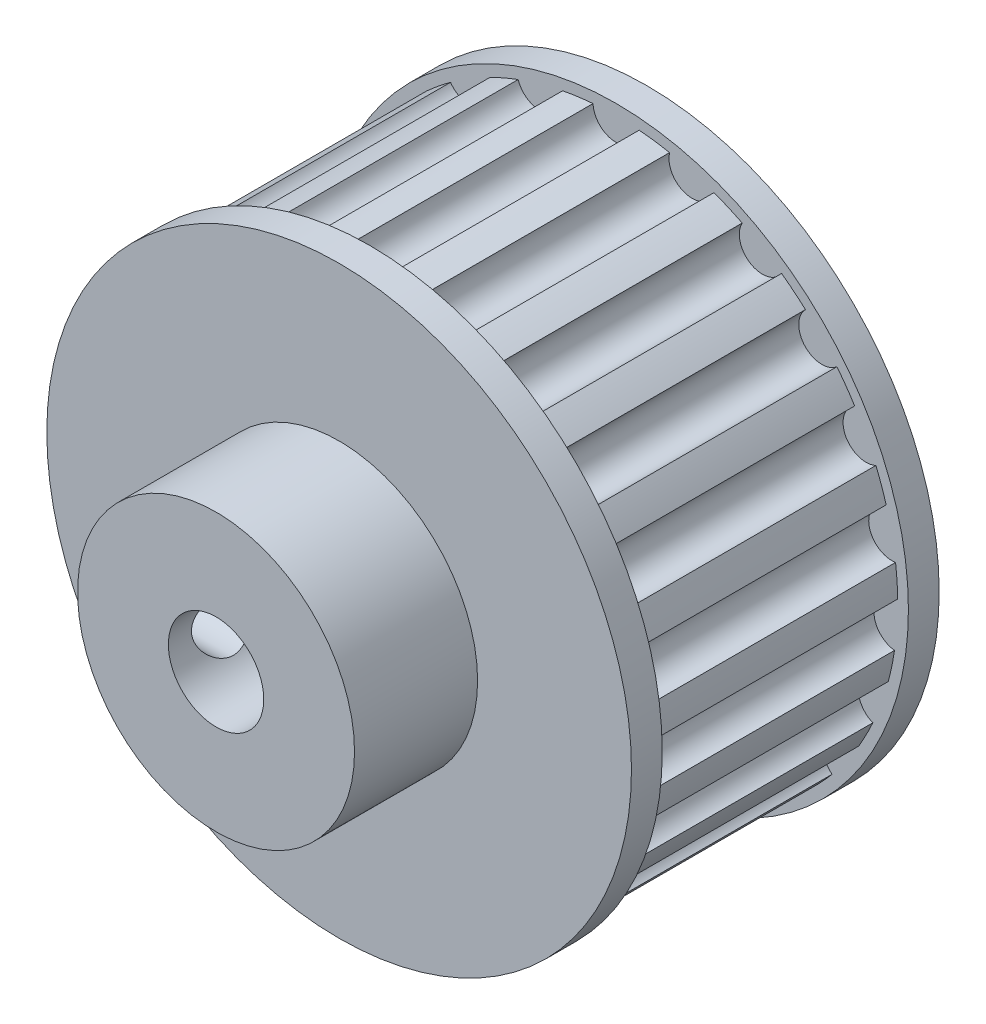
SolidWorks part; units mm, degrees
ref_plane "Спереди" through (0, 0, 0) normal (0, 0, 1) x (1, 0, 0)
ref_plane "Сверху" through (0, 0, 0) normal (0, 1, 0) x (1, 0, 0)
ref_plane "Справа" through (0, 0, 0) normal (1, 0, 0) x (0, 0, -1)
sketch "Эскиз1" plane through (0, 0, 0) normal (0, 0, 1) x (1, 0, 0)
  arc A0 (-1.4987, 18.241) -> (-3.4782, 17.969) centre (0, 0) ccw
  arc A1 (-1.4987, 18.241) -> (1.4987, 18.241) centre (0, 18.3025) ccw
  arc A2 (3.4782, 17.969) -> (6.3645, 17.1603) centre (4.938, 17.6238) ccw
  arc A3 (8.1972, 16.3642) -> (10.7583, 14.8068) centre (9.5097, 15.638) ccw
  arc A4 (12.3082, 13.5458) -> (14.3542, 11.3551) centre (13.3761, 12.4924) ccw
  arc A5 (15.5064, 9.7228) -> (16.8855, 7.0614) centre (16.2505, 8.4203) ccw
  arc A6 (17.5546, 5.1786) -> (18.1644, 2.2439) centre (17.9197, 3.7238) ccw
  arc A7 (18.3008, 0.2504) -> (18.0962, -2.7401) centre (18.2598, -1.249) ccw
  arc A8 (17.6897, -4.6963) -> (16.6859, -7.5208) centre (17.2457, -6.1291) ccw
  arc A9 (15.7667, -9.2948) -> (14.0381, -11.7437) centre (14.9526, -10.5547) ccw
  arc A10 (12.6743, -13.2039) -> (10.3491, -15.0956) centre (11.5505, -14.1975) ccw
  arc A11 (8.6419, -16.1338) -> (5.8926, -17.328) centre (7.2917, -16.7873) ccw
  arc A12 (3.9686, -17.8671) -> (0.999, -18.2752) centre (2.4922, -18.132) ccw
  arc A13 (-0.999, -18.2752) -> (-3.9686, -17.8671) centre (-2.4922, -18.132) ccw
  arc A14 (-5.8926, -17.328) -> (-8.6419, -16.1338) centre (-7.2917, -16.7873) ccw
  arc A15 (-10.3491, -15.0956) -> (-12.6743, -13.2039) centre (-11.5505, -14.1975) ccw
  arc A16 (-14.0381, -11.7437) -> (-15.7667, -9.2948) centre (-14.9526, -10.5547) ccw
  arc A17 (-16.6859, -7.5208) -> (-17.6897, -4.6963) centre (-17.2457, -6.1291) ccw
  arc A18 (-18.0962, -2.7401) -> (-18.3008, 0.2504) centre (-18.2598, -1.249) ccw
  arc A19 (-18.1644, 2.2439) -> (-17.5546, 5.1786) centre (-17.9197, 3.7238) ccw
  arc A20 (3.4782, 17.969) -> (1.4987, 18.241) centre (0, 0) ccw
  arc A21 (8.1972, 16.3642) -> (6.3645, 17.1603) centre (0, 0) ccw
  arc A22 (12.3082, 13.5458) -> (10.7583, 14.8068) centre (0, 0) ccw
  arc A23 (15.5064, 9.7228) -> (14.3542, 11.3551) centre (0, 0) ccw
  arc A24 (17.5546, 5.1786) -> (16.8855, 7.0614) centre (0, 0) ccw
  arc A25 (18.3008, 0.2504) -> (18.1644, 2.2439) centre (0, 0) ccw
  arc A26 (17.6897, -4.6963) -> (18.0962, -2.7401) centre (0, 0) ccw
  arc A27 (15.7667, -9.2948) -> (16.6859, -7.5208) centre (0, 0) ccw
  arc A28 (12.6743, -13.2039) -> (14.0381, -11.7437) centre (0, 0) ccw
  arc A29 (8.6419, -16.1338) -> (10.3491, -15.0956) centre (0, 0) ccw
  arc A30 (3.9686, -17.8671) -> (5.8926, -17.328) centre (0, 0) ccw
  arc A31 (-0.999, -18.2752) -> (0.999, -18.2752) centre (0, 0) ccw
  arc A32 (-5.8926, -17.328) -> (-3.9686, -17.8671) centre (0, 0) ccw
  arc A33 (-10.3491, -15.0956) -> (-8.6419, -16.1338) centre (0, 0) ccw
  arc A34 (-14.0381, -11.7437) -> (-12.6743, -13.2039) centre (0, 0) ccw
  arc A35 (-16.6859, -7.5208) -> (-15.7667, -9.2948) centre (0, 0) ccw
  arc A36 (-18.0962, -2.7401) -> (-17.6897, -4.6963) centre (0, 0) ccw
  arc A37 (-18.1644, 2.2439) -> (-18.3008, 0.2504) centre (0, 0) ccw
  arc A38 (-16.8855, 7.0614) -> (-15.5064, 9.7228) centre (-16.2505, 8.4203) ccw
  arc A39 (-14.3542, 11.3551) -> (-12.3082, 13.5458) centre (-13.3761, 12.4924) ccw
  arc A40 (-10.7583, 14.8068) -> (-8.1972, 16.3642) centre (-9.5097, 15.638) ccw
  arc A41 (-6.3645, 17.1603) -> (-3.4782, 17.969) centre (-4.938, 17.6238) ccw
  arc A42 (-6.3645, 17.1603) -> (-8.1972, 16.3642) centre (0, 0) ccw
  arc A43 (-10.7583, 14.8068) -> (-12.3082, 13.5458) centre (0, 0) ccw
  arc A44 (-14.3542, 11.3551) -> (-15.5064, 9.7228) centre (0, 0) ccw
  arc A45 (-16.8855, 7.0614) -> (-17.5546, 5.1786) centre (0, 0) ccw
  point P62 (0, 0)
  dimension "D1" = 36.605
  dimension "D2" = 3
  dimension "D3" = 23
extrude "Бобышка-Вытянуть1" add sketch "Эскиз1" along normal blind 16
sketch "Эскиз2" plane through (0, 0, 0) normal (0, 0, -1) x (-1, 0, 0)
  circle A0 centre (0, 0) radius 19
  dimension "D1" = 38
extrude "Бобышка-Вытянуть2" add sketch "Эскиз2" along normal blind 2
sketch "Эскиз3" plane through (0, 0, 16) normal (0, 0, 1) x (1, 0, 0)
  circle A0 centre (0, 0) radius 19
  dimension "D1" = 38
extrude "Бобышка-Вытянуть3" add sketch "Эскиз3" along normal blind 2
sketch "Эскиз4" plane through (0, 0, 18) normal (0, 0, 1) x (1, 0, 0)
  circle A0 centre (0, 0) radius 9
  circle A1 centre (0, 0) radius 3.1
  dimension "D1" = 18
  dimension "D2" = 6.2
extrude "Бобышка-Вытянуть4" add sketch "Эскиз4" along normal blind 8
sketch "Эскиз5" plane through (0, 0, 0) normal (1, 0, 0) x (0, 0, -1)
  line L0 (0, 0) -> (-30.4299, 0) construction
  line L1 (-26, 9) -> (-26, -9) construction
  circle A0 centre (-22.5, 0) radius 2
  dimension "D1" = 4
  dimension "D2" = 3.5
extrude "Вырез-Вытянуть1" cut sketch "Эскиз5" against normal through all
